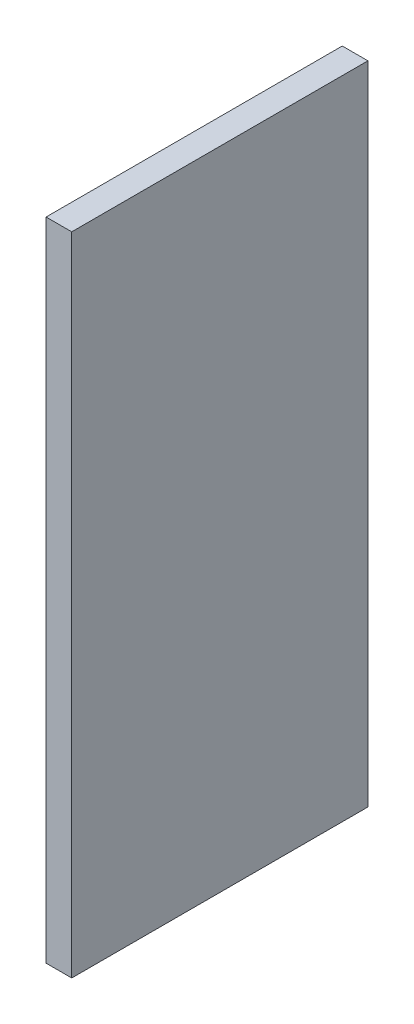
SolidWorks part; units mm, degrees
material "Oak"
ref_plane "Front Plane" through (0, 0, 0) normal (0, 0, 1) x (1, 0, 0)
ref_plane "Top Plane" through (0, 0, 0) normal (0, 1, 0) x (1, 0, 0)
ref_plane "Right Plane" through (0, 0, 0) normal (1, 0, 0) x (0, 0, -1)
sketch "Sketch1" plane through (0, 0, 0) normal (1, 0, 0) x (0, 0, -1)
  line L1 (-27.5, -60) -> (27.5, -60)
  line L2 (-27.5, -60) -> (-27.5, 60)
  line L3 (-27.5, 60) -> (27.5, 60)
  line L4 (27.5, -60) -> (27.5, 60)
  line L5 (-27.5, -60) -> (27.5, 60) construction
  line L6 (-27.5, 60) -> (27.5, -60) construction
  point P1 (0, 0)
  dimension "D1" = 120
  dimension "D2" = 55
extrude "Boss-Extrude1" add sketch "Sketch1" along normal blind 4.7625
